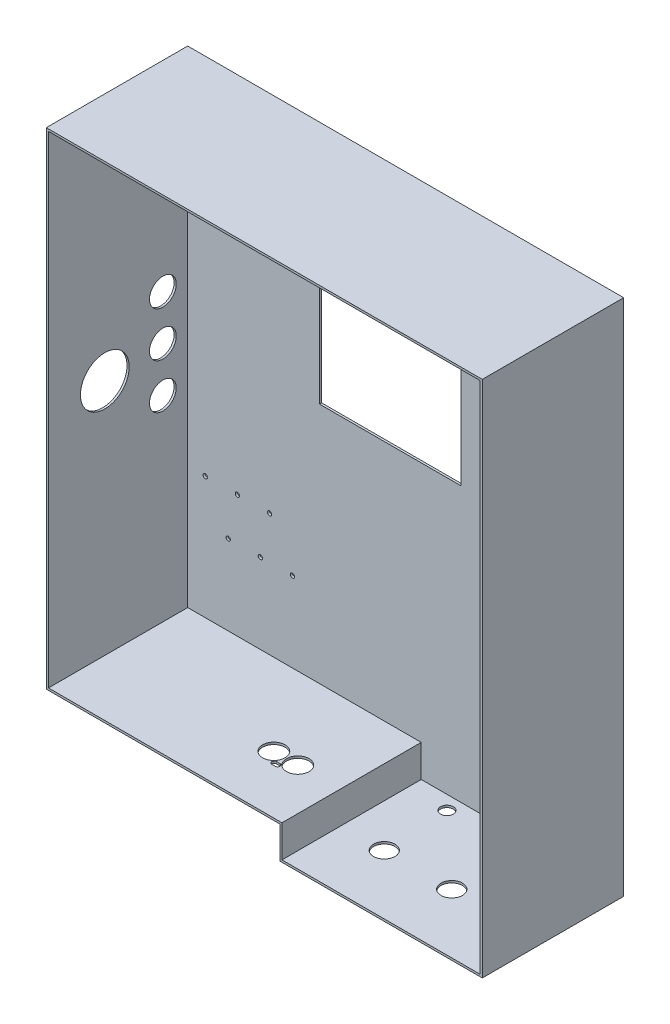
SolidWorks part; units mm, degrees
material "Zoltek Panex 33"
ref_plane "Płaszczyzna XY" through (0, 0, 0) normal (0, 0, 1) x (1, 0, 0)
ref_plane "Płaszczyzna XZ" through (0, 0, 0) normal (0, 1, 0) x (1, 0, 0)
ref_plane "Płaszczyzna YZ" through (0, 0, 0) normal (1, 0, 0) x (0, 0, -1)
ref_plane "Płaszczyzna1" through (0, 0, 464.2832) normal (0, 0, 1) x (1, 0, 0)
ref_plane "Płaszczyzna2" through (0, 0, 434.2832) normal (0, 0, 1) x (1, 0, 0)
sketch "Szkic1" plane through (0, 0, 434.2832) normal (0, 0, 1) x (1, 0, 0)
  line L0 (-977.2915, 225) -> (-977.2915, -255)
  line L1 (-1380.2915, 225) -> (-977.2915, 225)
  line L2 (-1380.2915, 225) -> (-1380.2915, -225)
  line L5 (-977.2915, -255) -> (-1162.2915, -255)
  line L6 (-1162.2915, -255) -> (-1162.2915, -225)
  line L7 (55, 0) -> (-55, 0) construction
  line L8 (-1162.2915, -225) -> (-1380.2915, -225)
  dimension "D2" = 403
  dimension "D3" = 185
  dimension "D4" = 225
  dimension "D5" = 480
  dimension "D6" = 977
  dimension "D7" = 30
extrude "Dodanie-wyciągnięcie1" add sketch "Szkic1" along normal blind 130
shell "Skorupa1" thickness 2
sketch "Szkic6" plane through (0, 0, 432.2832) normal (0, 0, -1) x (-1, 0, 0)
  line L0 (975.2915, 227) -> (1382.2915, 227) construction
  line L1 (1125.2915, 207) -> (1257.2915, 207)
  line L2 (1125.2915, 207) -> (1125.2915, 1)
  line L3 (1125.2915, 1) -> (1257.2915, 1)
  line L4 (1257.2915, 207) -> (1257.2915, 1)
  line L5 (975.2915, -257) -> (975.2915, 227) construction
  dimension "D1" = 20
  dimension "D2" = 150
  dimension "D3" = 132
  dimension "D4" = 206
extrude "Wytnij-wyciągnięcie1" cut sketch "Szkic6" against normal up to next
sketch "Szkic8" plane through (0, -257, 0) normal (0, -1, 0) x (1, 0, 0)
  line L0 (-1045.2915, 447.2832) -> (-1125.2915, 447.2832)
  line L1 (-975.2915, 564.2832) -> (-975.2915, 432.2832) construction
  line L2 (-1164.2915, 432.2832) -> (-975.2915, 432.2832) construction
  line L3 (-1122.2915, 508.7832) -> (-1059.2915, 508.7832) construction
  line L4 (-1164.2915, 564.2832) -> (-1164.2915, 432.2832) construction
  line L5 (-1164.2915, 564.2832) -> (-975.2915, 564.2832) construction
  circle A0 centre (-1122.2915, 508.7832) radius 10
  circle A1 centre (-1059.2915, 508.7832) radius 10
  point P2 (-1085.2915, 447.2832)
  dimension "D4" = 20
  dimension "D1" = 40
  dimension "D2" = 70
  dimension "D3" = 15
  dimension "D5" = 63
  dimension "D6" = 42
  dimension "D7" = 55.5
hole_wizard "Otwory ustalające Ø12.0mm1" positions "Szkic 3D1" profile "Szkic9" hole size "Ø12.0" standard "ISO"
sketch3d "Szkic 3D1"
  point P0 (-1125.2915, -257, 447.2832)
  point P3 (-1085.2915, -257, 447.2832)
  point P6 (-1045.2915, -257, 447.2832)
sketch "Szkic9" plane through (-1125.2915, -257, 447.2832) normal (1, 0, 0) x (0, 0, -1)
  line L0 (0, 0) -> (0, 2)
  line L1 (0, 2) -> (6, 2)
  line L2 (6, 2) -> (6, 0)
  line L5 (6, 0) -> (0, 0)
  line L11 (0, -6.35) -> (0, 107.95) construction
  dimension "Średnica otworu na wylot" = 12
  dimension "Głębokość otworu na wylot" = 2
sketch "Szkic10" plane through (-1382.2915, 0, 0) normal (-1, 0, 0) x (0, 0, 1)
  line L0 (457.4832, 42) -> (457.4832, -42) construction
  line L2 (432.2832, 227) -> (432.2832, -227) construction
  line L3 (564.2832, -227) -> (432.2832, -227) construction
  circle A0 centre (457.4832, 42) radius 12.5
  circle A1 centre (457.4832, 0) radius 12.5
  circle A2 centre (457.4832, -42) radius 12.5
  circle A3 centre (511.6832, -3) radius 22.75
  point P10 (0, 0)
  point P13 (511.6832, -24.2141)
  dimension "D1" = 25
  dimension "D2" = 45.5
  dimension "D3" = 42
  dimension "D4" = 3
  dimension "D5" = 25.2
  dimension "D6" = 54.2
  dimension "D7" = 185
extrude "Wytnij-wyciągnięcie2" cut sketch "Szkic10" against normal blind 10
extrude "Wytnij-wyciągnięcie3" cut sketch "Szkic8" against normal blind 10
sketch "Szkic11" plane through (0, 0, 432.2832) normal (0, 0, -1) x (-1, 0, 0)
  line L0 (1382.2915, 227) -> (1382.2915, -227) construction
  line L1 (1382.2915, -227) -> (1164.2915, -227) construction
  circle A0 centre (1363.8915, -110.6) radius 2
  circle A1 centre (1342.4915, -150.3) radius 2
  circle A2 centre (1312.4915, -150.3) radius 2
  circle A3 centre (1333.8915, -110.6) radius 2
  circle A4 centre (1282.4915, -150.3) radius 2
  circle A5 centre (1303.8915, -110.6) radius 2
  dimension "D1" = 4
  dimension "D2" = 4
  dimension "D8" = 30
  dimension "D3" = 18.4
  dimension "D4" = 39.7
  dimension "D5" = 21.4
  dimension "D6" = 76.7
  dimension "D7" = 3
extrude "Wytnij-wyciągnięcie4" cut sketch "Szkic11" against normal blind 10
sketch "Szkic12" plane through (0, -225, 0) normal (0, 1, 0) x (1, 0, 0)
  line L0 (-1201.5215, -510.2832) -> (-1223.8715, -510.2832) construction
  line L1 (-1212.6965, -510.2832) -> (-1212.6965, -519.5332) construction
  line L2 (-1380.2915, -564.2832) -> (-1162.2915, -564.2832) construction
  line L3 (-1162.2915, -564.2832) -> (-1162.2915, -434.2832) construction
  line L4 (-1211.1965, -519.5332) -> (-1214.1965, -519.5332) construction
  line L5 (-1211.1965, -521.7832) -> (-1214.1965, -521.7832)
  line L6 (-1211.1965, -517.2832) -> (-1214.1965, -517.2832)
  circle A0 centre (-1201.5215, -510.2832) radius 10.5
  circle A1 centre (-1223.8715, -510.2832) radius 10.5
  arc A2 (-1211.1965, -521.7832) -> (-1211.1965, -517.2832) centre (-1211.1965, -519.5332) ccw
  arc A3 (-1214.1965, -517.2832) -> (-1214.1965, -521.7832) centre (-1214.1965, -519.5332) ccw
  point P12 (-1212.6965, -519.5332)
  dimension "D1" = 21
  dimension "D2" = 22.35
  dimension "D3" = 54
  dimension "D4" = 39.23
  dimension "D5" = 7
  dimension "D6" = 3
  dimension "D7" = 4.5
extrude "Wytnij-wyciągnięcie5" cut sketch "Szkic12" against normal blind 10
